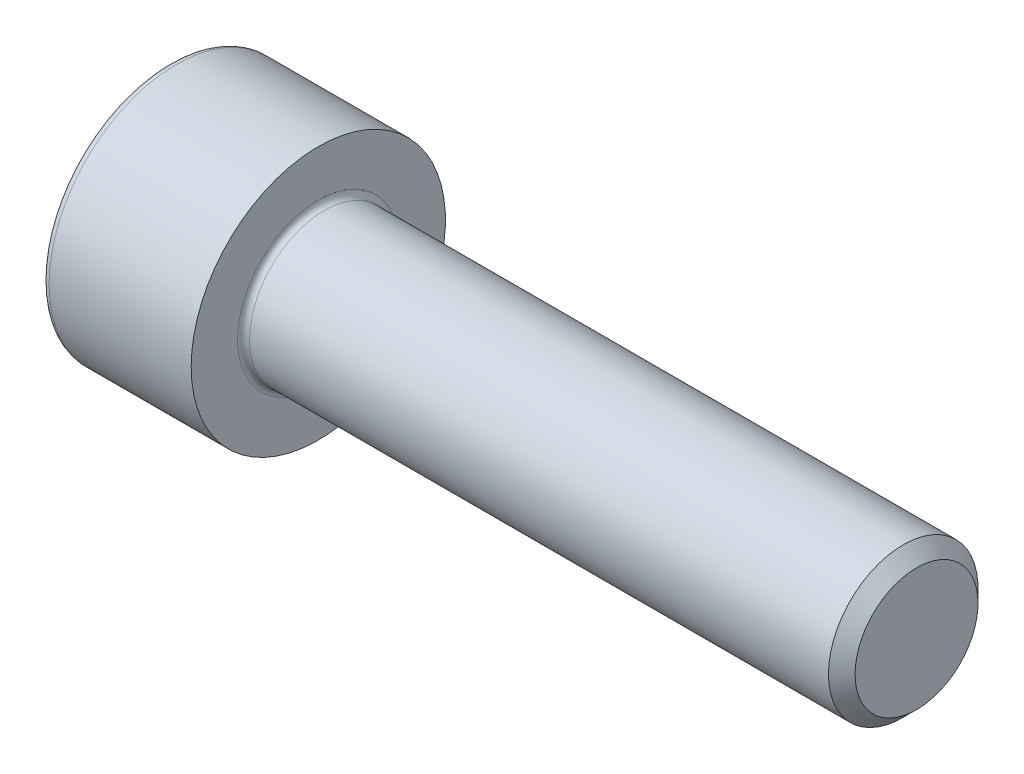
SolidWorks part; units mm, degrees
revolve "Base-Revolve" add sketch "BodySke"
sketch "BodySke" plane through (0, 0, 0) normal (0, 0, 1) x (1, 0, 0)
  line L0 (0, 0) -> (0, 4.25)
  line L1 (0, 4.25) -> (5, 4.25)
  line L2 (5, 4.25) -> (5, 2.5)
  line L3 (5, 2.5) -> (24.555, 2.5)
  line L4 (25, 2.055) -> (25, 0)
  line L5 (25, 0) -> (0, 0)
  line L6 (-31.75, 0) -> (127, 0) construction
  line L8 (25, 2.055) -> (24.555, 2.5)
  line L10 (25, -2.055) -> (24.555, -2.5) construction
  line L11 (5.8, 9.525) -> (5.8, 3.175) construction
  line L12 (5, 9.525) -> (5, 3.175) construction
  line L13 (-35, 9.525) -> (-35, 3.175) construction
  dimension "Head_ht" = 5
  dimension "Length" = 20
  dimension "Body_ch_ang" = 45
  dimension "Diameter" = 5
  dimension "Minor_dia" = 4.11
  dimension "Advance" = 0.8
  dimension "Thread_nom" = 20
  dimension "Thread_length" = 60
  dimension "Head_dia" = 8.5
cosmetic thread "ThreadCosmetic" [suppressed]
fillet "Fillet1" radius 0.2 1 edges at (5, 0, 2.5)
fillet "Fillet2" radius 0.25 1 edges at (0, 0, 4.25)
ref_plane "Plane1" through (0, 0, 0) normal (0, 0, 1) x (1, 0, 0)
ref_plane "Plane2" through (0, 0, 0) normal (0, 1, 0) x (1, 0, 0)
ref_plane "Plane3" through (0, 0, 0) normal (1, 0, 0) x (0, 0, -1)
sketch "Sketch2" plane through (0, 0, 0) normal (0, 0, 1) x (1, 0, 0)
  line L0 (0, 2.042) -> (2.5, 2.042)
  line L1 (2.5, 2.042) -> (3.6789, 0)
  line L2 (-31.75, 0) -> (127, 0) construction
  line L3 (3.6789, 0) -> (0, 0)
  line L4 (0, 0) -> (0, 2.042)
  line L6 (0, 0) -> (47.625, 0) construction
  dimension "D1" = 2.042
  dimension "D2" = 60
  dimension "Depth" = 2.5
revolve "Hex-PreBroach" cut sketch "Sketch2" angle 360 about L6
sketch "Sketch3" plane through (0, 0, 0) normal (-1, 0, 0) x (0, 0.5, 0.866)
  line L0 (1.1789, 2.042) -> (-1.1789, 2.042)
  line L1 (-1.1789, 2.042) -> (-2.3579, 0)
  line L2 (1.1789, 2.042) -> (2.3579, 0)
  line L3 (1.1789, -2.042) -> (2.3579, 0)
  line L4 (1.1789, -2.042) -> (-1.1789, -2.042)
  line L5 (-1.1789, -2.042) -> (-2.3579, 0)
  dimension "D1" = 2.042
  dimension "D2" = 2.042
  dimension "Hex_size" = 4.084
extrude "Hex" cut sketch "Sketch3" against normal blind 2.5
sketch "ThdSchSke" plane through (0, 0, 0) normal (0, 0, 1) x (1, 0, 0)
  line L0 (7.4, -2.055) -> (7.0884, -2.5)
  line L1 (7.4, -2.055) -> (7.7116, -2.5)
  line L2 (7.7116, -2.5) -> (7.7116, -3.125)
  line L3 (-3.175, 0) -> (5.1513, 0) construction
  line L4 (0, 4) -> (0, -4) construction
  line L5 (7.7116, -3.125) -> (7.0884, -3.125)
  line L6 (7.0884, -3.125) -> (7.0884, -2.5)
  dimension "Thread_minor" = 4.11
  dimension "Diameter" = 5
  dimension "Start" = 7.4
revolve "ThreadSchematic" [suppressed] cut sketch "ThdSchSke" angle 360 about L3
pattern_linear "ThdSchPat" [suppressed]
equation "\"D2@Sketch3\" = \"Hex_size@Sketch3\" / 2"
equation "\"D1@Sketch3\" = \"Hex_size@Sketch3\" / 2"
equation "\"D1@Sketch2\" = \"Hex_size@Sketch3\" / 2"
equation "\"Thread_minor@ThreadCosmetic\"  =  \"Minor_dia@BodySke\""
equation "\"Depth@Sketch2\" =  \"Key_eng@Hex\""
equation "\"Thread_length@ThreadCosmetic\" = ((sgn( (\"Length@BodySke\" - \"Advance@BodySke\" * 3.0) - \"Thread_nom@BodySke\" )-1)*( (\"Length@BodySke\" - \"Advance@BodySke\" * 3.0) - \"Thread_nom@BodySke\" ))/-2+ \"Thread_nom@BodySke\""
equation "\"Thread_minor@ThdSchSke\" = \"Minor_dia@BodySke\""
equation "\"Diameter@ThdSchSke\" = \"Diameter@BodySke\""
equation "\"Overcut@ThdSchSke\" = \"Diameter@BodySke\" * 1.25"
equation "\"Start@ThdSchSke\" = \"Head_ht@BodySke\" + \"Length@BodySke\" - \"Thread_length@ThreadCosmetic\"  '---Non-countersunk---"
equation "\"Num_threads@ThdSchPat\" = int( \"Thread_length@ThreadCosmetic\" / \"Advance@BodySke\" + 0.999 )  + 1"
equation "\"Advance@ThdSchPat\" = \"Thread_length@ThreadCosmetic\" /  (\"Num_threads@ThdSchPat\" - 1) 'relax it"
equation "\"Num_threads@ThdSchPat\" = \"Num_threads@ThdSchPat\" - sgn( \"Num_threads@ThdSchPat\" - 1) '---chamfered tips only---"
